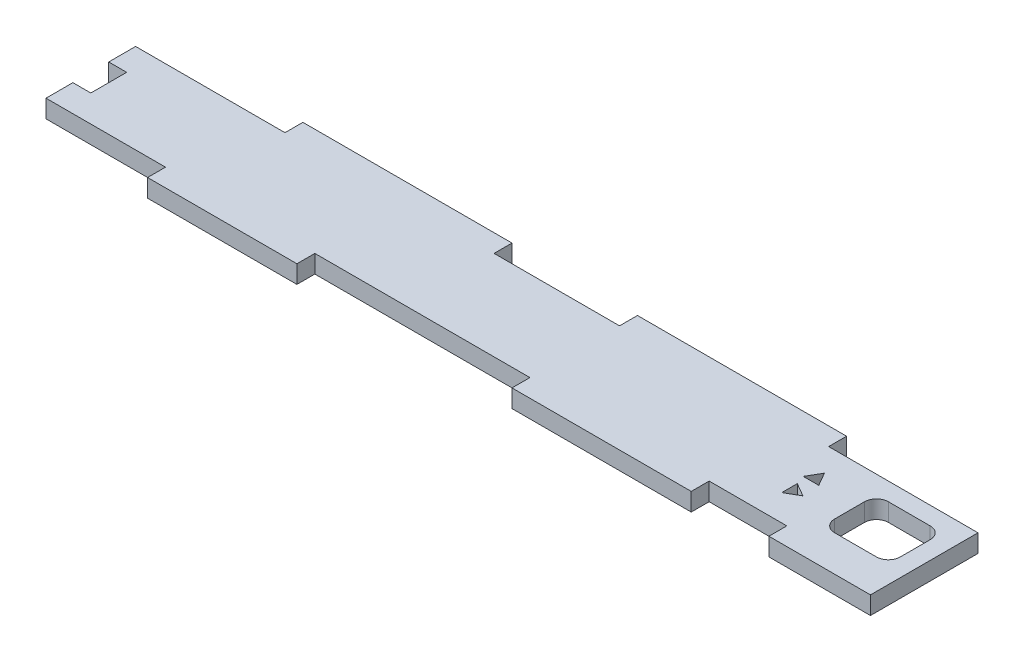
SolidWorks part; units mm, degrees
material "Acrylic (Medium-high impact)"
ref_plane "Plano frontal" through (0, 0, 0) normal (0, 0, 1) x (1, 0, 0)
ref_plane "Plano superior" through (0, 0, 0) normal (0, 1, 0) x (1, 0, 0)
ref_plane "Plano direito" through (0, 0, 0) normal (1, 0, 0) x (0, 0, -1)
sketch "Sketch1" plane through (0, 0, 0) normal (0, 1, 0) x (1, 0, 0)
  line L1 (-70.5, 7.5) -> (70.5, 7.5)
  line L2 (-70.5, 7.5) -> (-70.5, -7.5)
  line L3 (-70.5, -7.5) -> (70.5, -7.5)
  line L4 (70.5, 7.5) -> (70.5, -7.5)
  point P4 (0, 7.5)
  point P6 (-70.5, 0)
  dimension "D1" = 141
  dimension "D2" = 15
extrude "Boss-Extrude1" add sketch "Sketch1" along normal mid plane 3
sketch "Sketch2" plane through (0, 0, 0) normal (0, 1, 0) x (1, 0, 0)
  line L0 (-70.5, 7.5) -> (-70.5, -7.5) construction
  line L5 (-70.5, -7.5) -> (70.5, -7.5) construction
  line L6 (10.5, -7.5) -> (40.5, -7.5)
  line L7 (10.5, -7.5) -> (10.5, -10.5)
  line L8 (10.5, -10.5) -> (40.5, -10.5)
  line L9 (40.5, -7.5) -> (40.5, -10.5)
  line L10 (70.5, -7.5) -> (70.5, 7.5) construction
  line L18 (70.5, -7.5) -> (53.5, -7.5)
  line L19 (70.5, -7.5) -> (70.5, -10.5)
  line L20 (70.5, -10.5) -> (53.5, -10.5)
  line L21 (53.5, -7.5) -> (53.5, -10.5)
  dimension "D1" = 3
  dimension "D2" = 30
  dimension "D3" = 81
  dimension "D4" = 13
extrude "Boss-Extrude2" add sketch "Sketch2" along normal mid plane 3
sketch "Sketch12" plane through (0, 0, 0) normal (0, 1, 0) x (1, 0, 0)
  line L0 (-70.5, -7.5) -> (10.5, -7.5) construction
  line L1 (-50.5, -7.5) -> (-25.5, -7.5)
  line L2 (-50.5, -7.5) -> (-50.5, -10.5)
  line L3 (-50.5, -10.5) -> (-25.5, -10.5)
  line L4 (-25.5, -7.5) -> (-25.5, -10.5)
  line L5 (10.5, -10.5) -> (40.5, -10.5) construction
  line L6 (-5.5, 7.5) -> (-5.5, -7.5) construction
  line L7 (70.5, 7.5) -> (-70.5, 7.5) construction
  line L8 (-70.5, 7.5) -> (-70.5, -7.5) construction
  line L9 (-5.5, 7.5) -> (-70.5, 7.5) construction
  line L10 (-38, 7.5) -> (-38, -7.5) construction
  point P18 (-38, -7.5)
  dimension "D2" = 25
  dimension "D3" = 20
  dimension "D4" = 20
extrude "Boss-Extrude3" add sketch "Sketch12" along normal mid plane 3
sketch "Sketch13" plane through (0, 0, 0) normal (0, 1, 0) x (1, 0, 0)
  line L10 (70.5, 7.5) -> (-70.5, 7.5) construction
  line L12 (-45.5, 7.5) -> (-10.5, 7.5)
  line L13 (-45.5, 7.5) -> (-45.5, 10.5)
  line L14 (-45.5, 10.5) -> (-10.5, 10.5)
  line L15 (-10.5, 7.5) -> (-10.5, 10.5)
  line L16 (70.5, -10.5) -> (70.5, 7.5) construction
  line L17 (10.5, 7.5) -> (45.5, 7.5)
  line L18 (10.5, 7.5) -> (10.5, 10.5)
  line L19 (10.5, 10.5) -> (45.5, 10.5)
  line L20 (45.5, 7.5) -> (45.5, 10.5)
  dimension "D1" = 35
  dimension "D2" = 3
  dimension "D3" = 25
  dimension "D4" = 21
extrude "Boss-Extrude4" add sketch "Sketch13" along normal mid plane 3
sketch "Sketch15" plane through (0, 0, 0) normal (0, 1, 0) x (1, 0, 0)
  line L0 (40.5, -7.5) -> (53.5, -7.5) construction
  line L1 (56.5, 4.5) -> (67.5, 4.5)
  line L2 (56.5, 4.5) -> (56.5, -4.5)
  line L3 (56.5, -4.5) -> (67.5, -4.5)
  line L4 (67.5, 4.5) -> (67.5, -4.5)
  line L6 (70.5, 7.5) -> (45.5, 7.5) construction
  line L7 (70.5, -10.5) -> (70.5, 7.5) construction
  dimension "D1" = 3
  dimension "D4" = 9
  dimension "D2" = 11
  dimension "D3" = 3
  dimension "D5" = 3
extrude "Cut-Extrude10" cut sketch "Sketch15" against normal through all both and the other way through all
fillet "Fillet4" radius 2 4 edges at (56.5, 0, -4.5) (67.5, 0, -4.5) (67.5, 0, 4.5) (56.5, 0, 4.5)
sketch "Sketch16" plane through (0, 0, 0) normal (0, 1, 0) x (1, 0, 0)
  line L0 (40.5, -7.5) -> (53.5, -7.5) construction
  line L7 (56.5, 2.5) -> (56.5, -2.5) construction
  line L9 (49, 3.299) -> (47.701, 1.049)
  line L10 (47.701, 1.049) -> (50.299, 1.049)
  line L11 (50.299, 1.049) -> (49, 3.299)
  line L16 (50.5, -1.799) -> (48.25, -0.5)
  line L17 (48.25, -0.5) -> (48.25, -3.0981)
  line L18 (48.25, -3.0981) -> (50.5, -1.799)
  circle A0 centre (49, 1.799) radius 1.5 construction
  circle A1 centre (49, -1.799) radius 1.5 construction
  dimension "D1" = 3
extrude "Cut-Extrude11" cut sketch "Sketch16" against normal through all both and the other way through all
sketch "Sketch17" plane through (0, 0, 0) normal (0, 1, 0) x (1, 0, 0)
  line L0 (-70.5, 7.5) -> (-70.5, -7.5) construction
  line L1 (-70.5, 3) -> (-67.5, 3)
  line L2 (-70.5, 3) -> (-70.5, -3)
  line L3 (-70.5, -3) -> (-67.5, -3)
  line L4 (-67.5, 3) -> (-67.5, -3)
  point P6 (-67.5, 0)
  dimension "D1" = 3
  dimension "D2" = 6
extrude "Cut-Extrude12" cut sketch "Sketch17" against normal through all both and the other way through all
